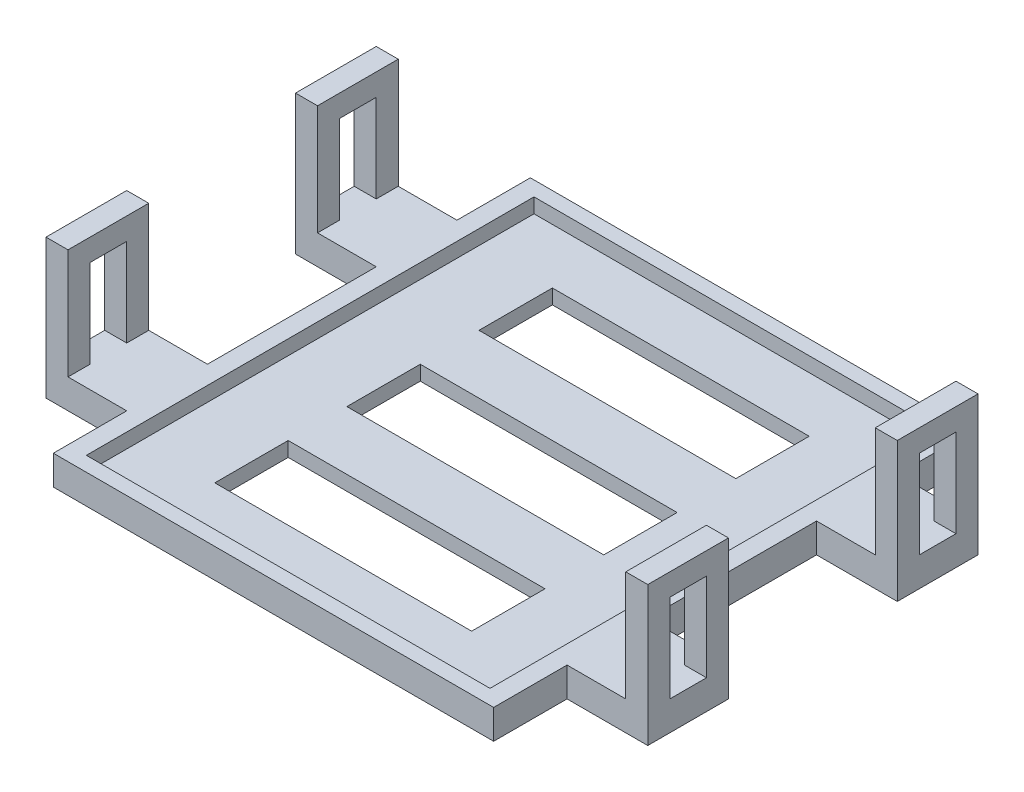
SolidWorks part; units mm, degrees
ref_plane "Alzado" through (0, 0, 0) normal (0, 0, 1) x (1, 0, 0)
ref_plane "Planta" through (0, 0, 0) normal (0, 1, 0) x (1, 0, 0)
ref_plane "Vista lateral" through (0, 0, 0) normal (1, 0, 0) x (0, 0, -1)
sketch "Croquis1" plane through (0, 0, 0) normal (0, 1, 0) x (1, 0, 0)
  line L0 (30, -32.5) -> (30, -22.5)
  line L1 (-30, 32.5) -> (30, 32.5)
  line L2 (30, -22.5) -> (30, -11.5) construction
  line L3 (-30, -32.5) -> (30, -32.5)
  line L4 (30, 11.5) -> (30, 22.5) construction
  line L5 (-30, 32.5) -> (30, -32.5) construction
  line L6 (-30, -32.5) -> (30, 32.5) construction
  line L7 (30, -22.5) -> (41, -22.5)
  line L8 (41, -22.5) -> (41, -11.5)
  line L9 (41, -11.5) -> (30, -11.5)
  line L10 (30, -11.5) -> (30, 11.5)
  line L11 (30, 11.5) -> (41, 11.5)
  line L12 (41, 11.5) -> (41, 22.5)
  line L13 (41, 22.5) -> (30, 22.5)
  line L14 (30, 22.5) -> (30, 32.5)
  line L15 (-30, 32.5) -> (-30, 22.5)
  line L16 (-30, 22.5) -> (-41, 22.5)
  line L17 (-41, 22.5) -> (-41, 11.5)
  line L18 (-41, 11.5) -> (-30, 11.5)
  line L19 (-30, 11.5) -> (-30, -11.5)
  line L20 (-30, -11.5) -> (-41, -11.5)
  line L21 (-41, -11.5) -> (-41, -22.5)
  line L22 (-41, -22.5) -> (-30, -22.5)
  line L23 (-30, -22.5) -> (-30, -32.5)
  line L24 (-30, 11.5) -> (-30, 22.5) construction
  line L25 (-30, -22.5) -> (-30, -11.5) construction
  point P0 (0, 0)
  dimension "D1" = 23
  dimension "D2" = 60
  dimension "D3" = 11
  dimension "D4" = 11
  dimension "D5" = 10
extrude "Saliente-Extruir1" add sketch "Croquis1" along normal blind 4
sketch "Croquis2" plane through (0, 4, 0) normal (0, 1, 0) x (1, 0, 0)
  line L0 (30, 32.5) -> (-30, 32.5) construction
  line L1 (-27.5, 30.5) -> (27.5, 30.5)
  line L2 (-27.5, 30.5) -> (-27.5, -30.5)
  line L3 (-27.5, -30.5) -> (27.5, -30.5)
  line L4 (27.5, 30.5) -> (27.5, -30.5)
  line L5 (-27.5, 30.5) -> (27.5, -30.5) construction
  line L6 (-27.5, -30.5) -> (27.5, 30.5) construction
  point P0 (0, 0)
  dimension "D1" = 2
  dimension "D2" = 55
extrude "Cortar-Extruir1" cut sketch "Croquis2" against normal blind 2
sketch "Croquis12" plane through (0, 4, 0) normal (0, 1, 0) x (1, 0, 0)
  line L0 (-41, 11.5) -> (-30, 11.5) construction
  line L1 (-41, 22.5) -> (-38, 22.5)
  line L2 (-41, 22.5) -> (-41, 11.5)
  line L3 (-41, 11.5) -> (-38, 11.5)
  line L4 (-38, 22.5) -> (-38, 11.5)
  line L5 (-41, -22.5) -> (-30, -22.5) construction
  line L6 (-41, -11.5) -> (-38, -11.5)
  line L7 (-41, -11.5) -> (-41, -22.5)
  line L8 (-41, -22.5) -> (-38, -22.5)
  line L9 (-38, -11.5) -> (-38, -22.5)
  line L10 (30, -22.5) -> (41, -22.5) construction
  line L11 (41, -11.5) -> (38, -11.5)
  line L12 (41, -11.5) -> (41, -22.5)
  line L13 (41, -22.5) -> (38, -22.5)
  line L14 (38, -11.5) -> (38, -22.5)
  line L15 (30, 11.5) -> (41, 11.5) construction
  line L16 (41, 22.5) -> (38, 22.5)
  line L17 (41, 22.5) -> (41, 11.5)
  line L18 (41, 11.5) -> (38, 11.5)
  line L19 (38, 22.5) -> (38, 11.5)
  dimension "D1" = 3
extrude "Saliente-Extruir2" add sketch "Croquis12" along normal blind 15
sketch "Croquis13" plane through (38, 0, 0) normal (-1, 0, 0) x (0, 0, 1)
  line L0 (-22.5, 4) -> (-11.5, 4) construction
  line L1 (-19.5, 4) -> (-14.5, 4)
  line L2 (-19.5, 4) -> (-19.5, 16)
  line L3 (-19.5, 16) -> (-14.5, 16)
  line L4 (-14.5, 4) -> (-14.5, 16)
  line L5 (-19.5, 4) -> (-22.5, 4) construction
  line L6 (-14.5, 4) -> (-11.5, 4) construction
  line L8 (-19.5, 16) -> (-19.5, 19) construction
  line L9 (-22.5, 19) -> (-11.5, 19) construction
  dimension "D1" = 3
extrude "Cortar-Extruir8" cut sketch "Croquis13" against normal through all and the other way through all
sketch "Croquis14" plane through (38, 0, 0) normal (-1, 0, 0) x (0, 0, 1)
  line L0 (11.5, 4) -> (22.5, 4) construction
  line L1 (14.5, 4) -> (19.5, 4)
  line L2 (14.5, 4) -> (14.5, 16)
  line L3 (14.5, 16) -> (19.5, 16)
  line L4 (19.5, 4) -> (19.5, 16)
  line L5 (14.5, 16) -> (14.5, 19) construction
  line L6 (11.5, 19) -> (22.5, 19) construction
  line L7 (14.5, 4) -> (11.5, 4) construction
  line L8 (19.5, 4) -> (22.5, 4) construction
  dimension "D1" = 3
extrude "Cortar-Extruir9" cut sketch "Croquis14" against normal through all and the other way through all
sketch "Croquis15" plane through (0, 0, 0) normal (0, 1, 0) x (1, 0, 0)
  line L0 (-27.5, 30.5) -> (-27.5, -30.5) construction
  line L1 (17.5, 5) -> (-17.5, 5)
  line L2 (17.5, 5) -> (17.5, -5)
  line L3 (17.5, -5) -> (-17.5, -5)
  line L4 (-17.5, 5) -> (-17.5, -5)
  line L5 (17.5, 5) -> (-17.5, -5) construction
  line L6 (17.5, -5) -> (-17.5, 5) construction
  line L7 (17.5, -13) -> (-17.5, -13)
  line L8 (17.5, -13) -> (17.5, -23)
  line L9 (17.5, -23) -> (-17.5, -23)
  line L10 (-17.5, -13) -> (-17.5, -23)
  line L15 (17.5, 13) -> (-17.5, 13)
  line L16 (17.5, 13) -> (17.5, 23)
  line L17 (17.5, 23) -> (-17.5, 23)
  line L18 (-17.5, 13) -> (-17.5, 23)
  line L23 (-17.5, -13) -> (-17.5, -5) construction
  line L24 (-17.5, 5) -> (-17.5, 13) construction
  point P0 (0, 0)
  dimension "D1" = 10
  dimension "D2" = 10
  dimension "D3" = 8
extrude "Cortar-Extruir10" cut sketch "Croquis15" along normal through all
